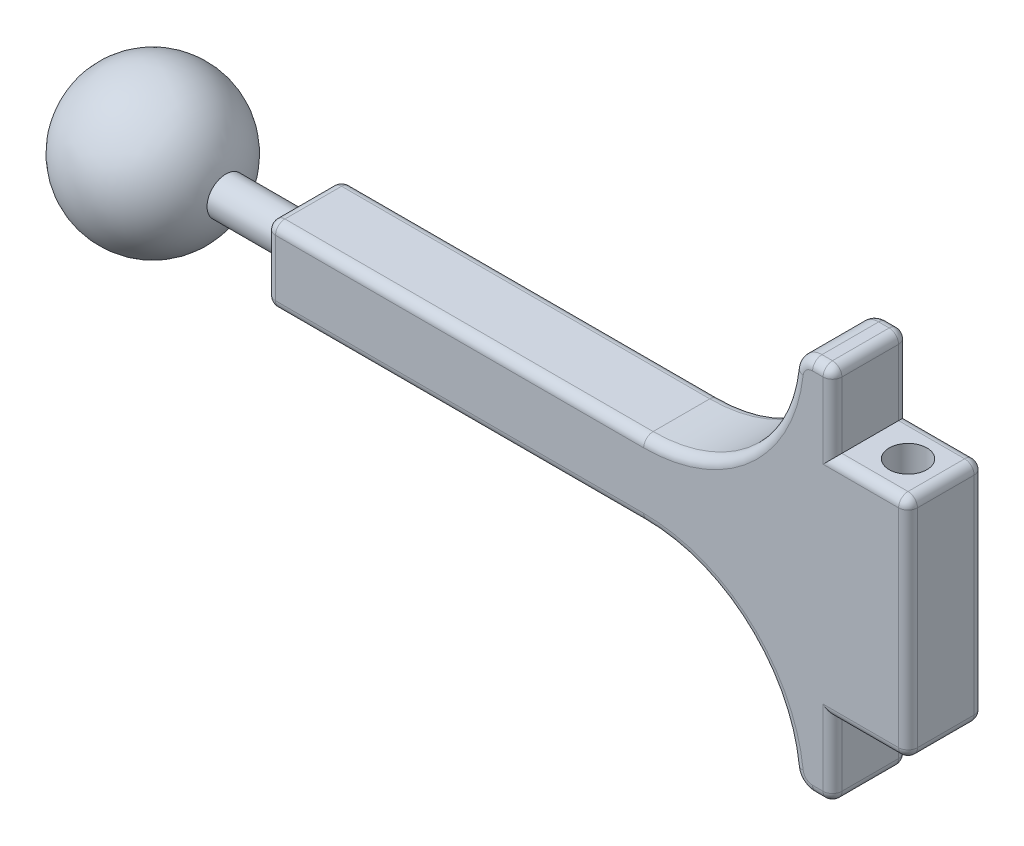
SolidWorks part; units mm, degrees
ref_plane "Front Plane" through (0, 0, 0) normal (0, 0, 1) x (1, 0, 0)
ref_plane "Top Plane" through (0, 0, 0) normal (0, 1, 0) x (1, 0, 0)
ref_plane "Right Plane" through (0, 0, 0) normal (1, 0, 0) x (0, 0, -1)
sketch "Sketch1" plane through (0, 0, 0) normal (0, 0, 1) x (1, 0, 0)
  line L0 (0, 25) -> (0, -25) construction
  line L1 (-100, 0) -> (5, 0) construction
  line L2 (5, 25) -> (5, -25) construction
  line L3 (-5, 25) -> (-5, -25) construction
  line L4 (-80, 5) -> (-30, 5)
  line L5 (-80, -5) -> (-30, -5)
  line L6 (-55, 5) -> (-55, -5) construction
  line L7 (-7.6393, 25) -> (5, 25) construction
  line L8 (-7.6393, -25) -> (5, -25) construction
  line L9 (-80, 5) -> (-80, -5)
  line L15 (-5, 25) -> (-5, 15)
  line L16 (-5, 15) -> (5, 15)
  line L17 (5, 15) -> (5, -15)
  line L18 (5, -15) -> (-5, -15)
  line L19 (-5, -15) -> (-5, -25)
  line L20 (-7.6393, 25) -> (-5, 25)
  line L21 (-7.6393, -25) -> (-5, -25)
  arc A0 (-30, 5) -> (-10.1238, 22.7778) centre (-30, 25) ccw
  arc A1 (-30, -5) -> (-10.1238, -22.7778) centre (-30, -25) cw
  arc A2 (-7.6393, 25) -> (-10.1238, 22.7778) centre (-7.6393, 22.5) ccw
  arc A3 (-10.1238, -22.7778) -> (-7.6393, -25) centre (-7.6393, -22.5) ccw
  point P8 (-5, 0)
  point P9 (0, 0)
  point P15 (5, 0)
  point P19 (-55, 0)
  point P22 (-55, 5)
  point P24 (-55, -5)
  dimension "D7" = 5
  dimension "D8" = 20
  dimension "D1" = 100
  dimension ".5" = 5
  dimension "D2" = 50
  dimension "D3" = 10
  dimension "D4" = 25
  dimension "D5" = 10
  dimension "D6" = 80
extrude "Boss-Extrude2" add sketch "Sketch1" along normal blind 10
sketch "Sketch2" plane through (-80, 0, 0) normal (-1, 0, 0) x (0, 0, 1)
  line L0 (10, 5) -> (0, -5) construction
  circle A0 centre (5, 0) radius 2.5
  dimension "D1" = 5
extrude "Boss-Extrude3" add sketch "Sketch2" along normal blind 20
sketch "Sketch3" plane through (-100, 0, 0) normal (-1, 0, 0) x (0, 0, 1)
  line L0 (5, 10) -> (5, -10)
  arc A0 (5, 10) -> (5, -10) centre (5, 0) ccw
  dimension "D1" = 20
revolve "Revolve1" add sketch "Sketch3" angle 360 about L0
sketch "Sketch4" plane through (0, 15, 0) normal (0, 1, 0) x (1, 0, 0)
  line L0 (-5, 0) -> (5, -10) construction
  circle A0 centre (0, -5) radius 2.5
  dimension "D1" = 5
extrude "Cut-Extrude1" cut sketch "Sketch4" against normal through all
fillet "Fillet1" radius 1.25 34 edges at (-80, 0, 0) (-80, -5, 5) (-80, 0, 10) (-80, 5, 5) (-6.3197, -25, 10) (-9.306, -24.3634, 10) (-16.6667, -10.0929, 10) (-6.3197, -25, 0) (-9.306, -24.3634, 0) (-16.6667, -10.0929, 0) (-6.3197, 25, 0) (-9.306, 24.3634, 0) (-16.6667, 10.0929, 0) (-6.3197, 25, 10) (-9.306, 24.3634, 10) (-16.6667, 10.0929, 10) (-55, -5, 10) (-55, -5, 0) (-55, 5, 0) (-55, 5, 10) (5, -15, 5) (0, -15, 0) (-5, -20, 0) (-5, -20, 10) (0, -15, 10) (-5, 20, 0) (-5, 20, 10) (5, 15, 5) (0, 15, 0) (0, 15, 10) (5, 0, 0) (5, 0, 10) (-5, -25, 5) (-5, 25, 5)
